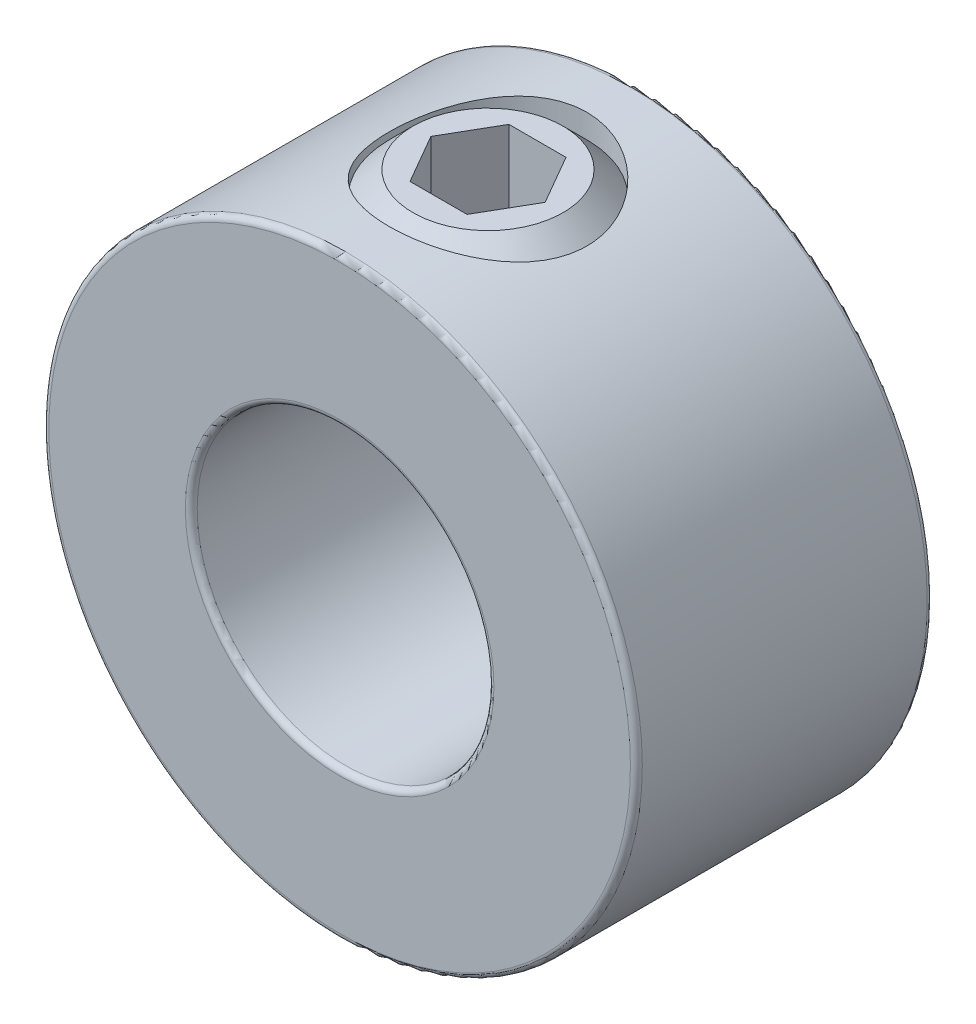
SolidWorks part; units mm, degrees
ref_plane "Front Plane" through (0, 0, 0) normal (0, 0, 1) x (1, 0, 0)
ref_plane "Top Plane" through (0, 0, 0) normal (0, 1, 0) x (1, 0, 0)
ref_plane "Right Plane" through (0, 0, 0) normal (1, 0, 0) x (0, 0, -1)
sketch "Sketch1" plane through (0, 0, 0) normal (0, 0, 1) x (1, 0, 0)
  circle A0 centre (0, 0) radius 9.525
  circle A1 centre (0, 0) radius 4.7625
  point P4 (9.525, 0)
  dimension "Bore Dia" = 9.525
  dimension "OD" = 19.05
extrude "Extrude1" add sketch "Sketch1" along normal mid plane 9.525
sketch "Sketch2" plane through (41.275, 0, 0) normal (0, -1, 0) x (0, 0, -1)
  line L0 (4.7625, -41.275) -> (-4.7625, -41.275) construction
  line L1 (-4.7625, -31.75) -> (-4.7625, -50.8) construction
  line L2 (4.7625, -50.8) -> (4.7625, -31.75) construction
  circle A0 centre (0, -41.275) radius 3.175
  point P7 (0, -44.45)
  dimension "Set Screw Dia" = 6.35
extrude "Cut-Extrude1" cut sketch "Sketch2" against normal through all
fillet "Fillet1" radius 0.1905 4 edges at (4.7625, 0, -4.7625) (4.7625, 0, 4.7625) (9.525, 0, -4.7625) (9.525, 0, 4.7625)
sketch "Sketch3" plane through (0, 0, 0) normal (0, 0, 1) x (1, 0, 0)
  line L0 (-2.4082, 4.7625) -> (-0.9202, 4.7625)
  line L1 (0, 5.6827) -> (-0.9202, 4.7625)
  line L2 (0, 5.6827) -> (0, 9.525)
  line L3 (0, 9.525) -> (-2.4082, 9.525)
  line L4 (-3.175, 5.5293) -> (-3.175, 8.7582)
  line L5 (0, 4.7625) -> (0, 0) construction
  line L6 (-3.175, 5.5293) -> (-3.175, 4.7625) construction
  line L7 (-3.175, 4.7625) -> (-2.4082, 4.7625) construction
  line L8 (-3.175, 8.7582) -> (-3.175, 9.525) construction
  line L9 (-2.4082, 4.7625) -> (-3.175, 5.5293)
  line L10 (-3.175, 8.7582) -> (-2.4082, 9.525)
  line L11 (-3.175, 9.525) -> (-2.4082, 9.525) construction
  line L12 (-0.9202, 4.7625) -> (0, 4.7625) construction
  line L13 (0, 4.7625) -> (0, 5.6827) construction
  circle A1 centre (0, 0) radius 4.7625 construction
  dimension "Screw Length" = 4.7625
  dimension "D2" = 0.7668
  dimension "D1" = 0.9202
revolve "Revolve1" add sketch "Sketch3" angle 360 about L5
sketch "Sketch4" plane through (3.3734, 9.525, 0) normal (0, -1, 0) x (0, 0, -1)
  line L1 (0, -1.5404) -> (-1.5875, -2.4569)
  line L2 (-1.5875, -2.4569) -> (-1.5875, -4.29)
  line L3 (-1.5875, -4.29) -> (0, -5.2065)
  line L4 (0, -5.2065) -> (1.5875, -4.29)
  line L5 (1.5875, -4.29) -> (1.5875, -2.4569)
  line L6 (1.5875, -2.4569) -> (0, -1.5404)
  circle A0 centre (0, -3.3734) radius 1.5875 construction
  circle A1 centre (0, -3.3734) radius 1.8331 construction
  dimension "D1" = 3.6662
  dimension "Hex Size" = 3.175
extrude "Cut-Extrude2" cut sketch "Sketch4" along normal blind 3.175
equation "\"D1@Fillet1\" = \"OD@Sketch1\"*.01"
equation "\"D1@Cut-Extrude2\" = \"Hex Size@Sketch4\""
equation "\"D2@Sketch3\" =(\"Set Screw Dia@Sketch2\"-\"D1@Sketch4\")/3.5"
equation "\"D1@Sketch3\" = \"D2@Sketch3\"*1.2"
